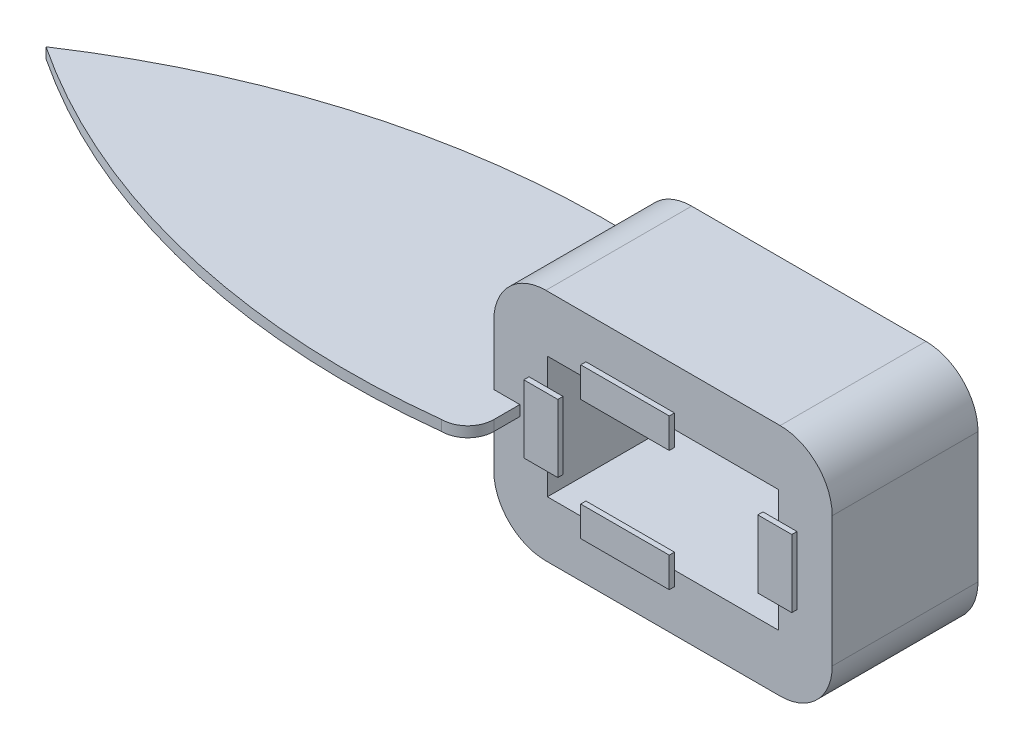
SolidWorks part; units mm, degrees
other "標示1"
sketch "草圖23" plane through (5.0653, 22.5, 33.0476) normal (0.0778, 0.9965, 0.0321) x (0.9968, -0.077, -0.0229)
other "標示2"
sketch "草圖24" plane through (5.0653, 22.5, -10) normal (0.0784, 0.9039, -0.4204) x (0.9626, 0.041, 0.2678)
other "標示3"
sketch "草圖25" plane through (-159.9347, 22.5, -10.9796) normal (0, 1, 0) x (1, 0, 0)
ref_plane "前基準面" through (0, 0, 0) normal (0, 0, 1) x (1, 0, 0)
ref_plane "上基準面" through (0, 0, 0) normal (0, 1, 0) x (1, 0, 0)
ref_plane "右基準面" through (0, 0, 0) normal (1, 0, 0) x (0, 0, -1)
sketch "草圖1" plane through (0, 0, 0) normal (0, 0, 1) x (1, 0, 0)
  line L0 (-9.02, 0) -> (7.9922, 0) construction
  line L2 (-59.9347, 22.5) -> (5.0653, 22.5)
  line L3 (-59.9347, 22.5) -> (-59.9347, -22.5)
  line L4 (-59.9347, -22.5) -> (5.0653, -22.5)
  line L5 (5.0653, 22.5) -> (5.0653, -22.5)
  dimension "D1" = 45
  dimension "D2" = 22.5
  dimension "D3" = 65
extrude "填料-伸長1" add sketch "草圖1" along normal blind 28
sketch "草圖2" plane through (0, 0, 0) normal (0, 0, 1) x (1, 0, 0)
  line L0 (-59.9347, 0) -> (5.361, 0) construction
  line L1 (-59.9347, 22.5) -> (-59.9347, -22.5) construction
  line L2 (-27.4347, 22.5) -> (-27.4347, -22.5) construction
  line L3 (5.0653, 22.5) -> (-59.9347, 22.5) construction
  line L4 (-59.9347, -22.5) -> (5.0653, -22.5) construction
  line L6 (-49.6347, 11.7) -> (-5.2347, 11.7)
  line L7 (-49.6347, 11.7) -> (-49.6347, -11.7)
  line L8 (-49.6347, -11.7) -> (-5.2347, -11.7)
  line L9 (-5.2347, 11.7) -> (-5.2347, -11.7)
  dimension "D1" = 44.4
  dimension "D2" = 23.4
  dimension "D3" = 10.3
  dimension "D4" = 10.8
extrude "除料-伸長1" cut sketch "草圖2" along normal blind 39
ref_plane "平面1" through (0, 0, 28) normal (0, 0, 1) x (1, 0, 0)
sketch "草圖3" plane through (0, 0, 28) normal (0, 0, 1) x (1, 0, 0)
  line L0 (-59.9347, 22.5) -> (-59.9347, -22.5) construction
  line L2 (-59.9347, 12) -> (-55.9347, 12)
  line L3 (-59.9347, 12) -> (-59.9347, -12)
  line L4 (-59.9347, -12) -> (-55.9347, -12)
  line L5 (-55.9347, 12) -> (-55.9347, -12)
  line L8 (-5.2347, -11.7) -> (-49.6347, -11.7) construction
  dimension "D1" = 4
  dimension "D2" = 24
  dimension "D3" = 0.3
ref_plane "平面2" through (-59.9347, 0, 0) normal (-1, 0, 0) x (0, 0, 1)
sketch "草圖6" plane through (0, 0, 28) normal (0, 0, 1) x (1, 0, 0)
  line L0 (-15.2347, 0.3) -> (5.0653, -22.5)
  line L1 (-5.2347, 11.7) -> (-5.2347, -11.7) construction
  line L2 (-5.2347, -11.7) -> (-49.6347, -11.7) construction
  line L3 (-15.2347, 0.3) -> (-15.2347, -22.5)
  line L4 (-59.9347, -22.5) -> (5.0653, -22.5) construction
  line L5 (-15.2347, -22.5) -> (5.0653, -22.5)
  dimension "D1" = 10
  dimension "D2" = 12
ref_plane "平面4" through (0, 0, 0) normal (0, 0, -1) x (-1, 0, 0)
fillet "圓角1" radius 10 1 edges at (-59.9347, -22.5, 14)
fillet "圓角2" radius 10 1 edges at (-59.9347, 22.5, 14)
fillet "圓角3" radius 10 1 edges at (5.0653, 22.5, 14)
fillet "圓角4" radius 10 1 edges at (5.0653, -22.5, 14)
ref_plane "平面6" through (0, 0, 29) normal (0, 0, 1) x (1, 0, 0)
sketch "草圖10" plane through (0, 0, 29) normal (0, 0, 1) x (1, 0, 0)
  line L6 (-49.6347, 0) -> (-4.2092, 0) construction
  line L7 (-49.6347, -11.7) -> (-49.6347, 11.7) construction
  line L8 (-27.4347, -11.7) -> (-27.4347, 19.297) construction
  line L9 (-5.2347, -11.7) -> (-49.6347, -11.7) construction
  line L11 (-49.6347, 6.5) -> (-53.1651, 6.5)
  line L14 (-53.1651, 6.5) -> (-53.1651, -6.5)
  line L17 (-49.6347, 6.5) -> (-46.6347, 6.5)
  line L18 (-46.6347, 6.5) -> (-46.6347, -6.5)
  line L20 (-42.2347, -11.7) -> (-42.2347, -8.7)
  line L25 (-42.2347, -11.7) -> (-42.2347, -14.4546)
  line L27 (-8.2347, 6.5) -> (-8.2347, -6.5)
  line L28 (-8.2347, -6.5) -> (-5.2347, -6.5)
  line L29 (-5.2347, -6.5) -> (-1.7043, -6.5)
  line L30 (-1.7043, 6.5) -> (-1.7043, -6.5)
  line L32 (-25.2347, 8.7) -> (-25.2347, 14.4546)
  line L33 (-25.2347, -14.4546) -> (-25.2347, -8.7)
  line L34 (-25.2347, -14.4546) -> (-42.2347, -14.4546)
  line L35 (-25.2347, -8.7) -> (-42.2347, -8.7)
  line L36 (-25.2347, 8.7) -> (-42.2347, 8.7)
  line L37 (-25.2347, 14.4546) -> (-42.2347, 14.4546)
  line L38 (-42.2347, 8.7) -> (-42.2347, 14.4546)
  line L39 (-46.6347, -6.5) -> (-53.1651, -6.5)
  line L40 (-1.7043, 6.5) -> (-8.2347, 6.5)
  dimension "D3" = 13
  dimension "D4" = 6.5
extrude "填料-伸長6" add sketch "草圖10" against normal blind 1 separate body
sketch "草圖19" plane through (0, 0, 0) normal (0, 1, 0) x (1, 0, 0)
  line L0 (-59.9347, 6.325) -> (-59.9347, -6.325) construction
  line L1 (-59.9347, 1.0971) -> (-54.9347, 1.0971)
  line L2 (-59.9347, 1.0971) -> (-59.9347, -29)
  line L3 (-59.9347, -29) -> (-54.9347, -29)
  line L4 (-54.9347, 1.0971) -> (-54.9347, -29)
  line L5 (-24.75, -29) -> (24.75, -29) construction
  dimension "D1" = 5
ref_plane "平面7" through (0, 0, 28) normal (0, 0, 1) x (1, 0, 0)
sketch "草圖20" plane through (0, 0, 28) normal (0, 0, 1) x (1, 0, 0)
  line L0 (-59.9347, 12.5) -> (-59.9347, -12.5) construction
  line L1 (-59.9347, 1) -> (-54.932, 1)
  line L2 (-59.9347, 1) -> (-59.9347, -1)
  line L3 (-59.9347, -1) -> (-54.932, -1)
  line L4 (-54.932, 1) -> (-54.932, -1)
  line L5 (-59.9347, 0) -> (-54.9347, 0) construction
  dimension "D1" = 5.0026
  dimension "D2" = 2
  dimension "D3" = 1
extrude "填料-伸長7" add sketch "草圖20" along normal blind 10
ref_plane "平面8" through (0, 0, 0) normal (0, 0, -1) x (-1, 0, 0)
sketch "草圖21" plane through (0, 0, 0) normal (0, 0, -1) x (-1, 0, 0)
  line L0 (59.9347, 0) -> (54.9347, 0) construction
  line L1 (54.9323, 1) -> (59.9347, 1)
  line L2 (54.9323, 1) -> (54.9323, -1)
  line L3 (54.9323, -1) -> (59.9347, -1)
  line L4 (59.9347, 1) -> (59.9347, -1)
  dimension "D1" = 5.0023
  dimension "D2" = 2
  dimension "D3" = 1
extrude "填料-伸長8" add sketch "草圖21" along normal blind 10
sketch "草圖22" plane through (0, 0, 0) normal (0, 1, 0) x (1, 0, 0)
  line L1 (-59.9347, 10) -> (-59.9347, -38)
  line L2 (-59.9347, -14) -> (-159.9347, -14) construction
  arc A2 (-159.9347, -14) -> (-59.9347, 10) centre (-77.0498, -139.0204) cw
  arc A3 (-159.9347, -14) -> (-59.9347, -38) centre (-77.0498, 111.0204) ccw
  dimension "D2" = 150
  dimension "D3" = 150
  dimension "D1" = 100
extrude "填料-伸長9" add sketch "草圖22" along normal blind 1 and the other way blind 1
fillet "圓角5" radius 5 1 edges at (-54.9323, 0, -10)
fillet "圓角6" radius 5 1 edges at (-54.932, 0, 38)
